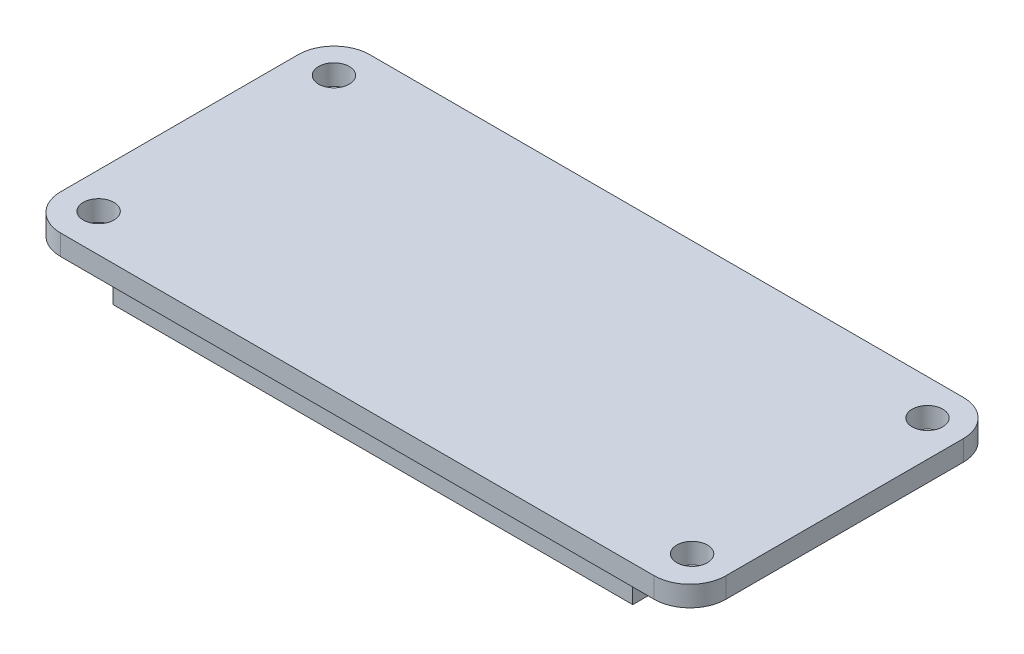
SolidWorks part; units mm, degrees
ref_plane "前基準面" through (0, 0, 0) normal (0, 0, 1) x (1, 0, 0)
ref_plane "上基準面" through (0, 0, 0) normal (0, 1, 0) x (1, 0, 0)
ref_plane "右基準面" through (0, 0, 0) normal (1, 0, 0) x (0, 0, -1)
sketch "草圖1" plane through (0, 0, 0) normal (0, 1, 0) x (1, 0, 0)
  line L1 (-32.5, 15.1) -> (32.5, 15.1)
  line L2 (-32.5, 15.1) -> (-32.5, -15.1)
  line L3 (-32.5, -15.1) -> (32.5, -15.1)
  line L4 (32.5, 15.1) -> (32.5, -15.1)
  line L5 (-32.5, 15.1) -> (32.5, -15.1) construction
  line L6 (-32.5, -15.1) -> (32.5, 15.1) construction
  point P0 (0, 0)
  dimension "D1" = 65
  dimension "D2" = 30.2
extrude "填料-伸長1" add sketch "草圖1" along normal blind 2
sketch "草圖2" plane through (0, 2, 0) normal (0, 1, 0) x (1, 0, 0)
  line L0 (32.5, 15.1) -> (-32.5, 15.1) construction
  line L1 (-32.5, 15.1) -> (-32.5, -15.1) construction
  line L2 (-32.5, -15.1) -> (32.5, -15.1) construction
  line L3 (0, 15.1) -> (0, -15.1) construction
  circle A0 centre (-29, 11.6) radius 1.5
  circle A1 centre (-29, -11.4) radius 1.5
  circle A2 centre (29, -11.4) radius 1.5
  circle A3 centre (29, 11.6) radius 1.5
  dimension "D1" = 3
  dimension "D2" = 3.5
  dimension "D3" = 3.5
  dimension "D4" = 3.7
extrude "除料-伸長1" cut sketch "草圖2" against normal through all
sketch "草圖3" plane through (0, 2, 0) normal (0, 1, 0) x (1, 0, 0)
  text T0 "UP"
fillet "圓角1" radius 3.5 4 edges at (-32.5, 1, -15.1) (-32.5, 1, 15.1) (32.5, 1, 15.1) (32.5, 1, -15.1)
sketch "草圖4" plane through (0, 0, 0) normal (0, -1, 0) x (1, 0, 0)
  line L0 (-29, 15.1) -> (29, 15.1) construction
  line L1 (-25.4, 13.6) -> (25.4, 13.6)
  line L2 (-25.4, 13.6) -> (-25.4, 8.52)
  line L3 (-25.4, 8.52) -> (25.4, 8.52)
  line L4 (25.4, 13.6) -> (25.4, 8.52)
  line L5 (-25.4, 13.6) -> (25.4, 8.52) construction
  line L6 (-25.4, 8.52) -> (25.4, 13.6) construction
  point P0 (0, 11.06)
  point P6 (0, 0)
  point P7 (0, 11.1684)
  dimension "D1" = 50.8
  dimension "D2" = 5.08
  dimension "D3" = 1.5
extrude "填料-伸長2" add sketch "草圖4" along normal blind 3
